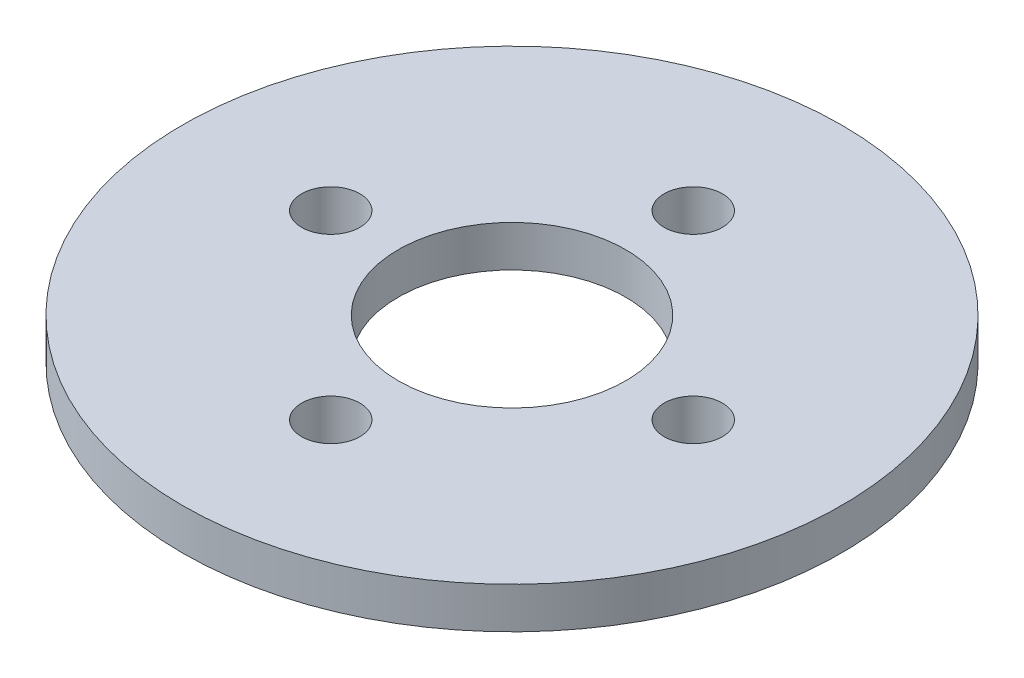
SolidWorks part; units mm, degrees
ref_plane "Front Plane" through (0, 0, 0) normal (0, 0, 1) x (1, 0, 0)
ref_plane "Top Plane" through (0, 0, 0) normal (0, 1, 0) x (1, 0, 0)
ref_plane "Right Plane" through (0, 0, 0) normal (1, 0, 0) x (0, 0, -1)
sketch "Sketch1" plane through (0, 0, 0) normal (0, 1, 0) x (1, 0, 0)
  circle A0 centre (0, 0) radius 25.4
  circle A1 centre (0, 0) radius 8.763
  dimension "D1" = 50.8
  dimension "D2" = 17.526
extrude "Boss-Extrude1" add sketch "Sketch1" along normal blind 3.175
hole_wizard "#8 Clearance Hole1" positions "Sketch2" profile "Sketch3" hole size "#8" standard "ANSI Inch" end condition through all
sketch "Sketch2" plane through (0, 3.175, 0) normal (0, 1, 0) x (1, 0, 0)
  circle A0 centre (0, 0) radius 13.97
  point P4 (0, 13.97)
  point P6 (-13.97, 0)
  point P8 (0, -13.97)
  point P10 (13.97, 0)
  dimension "D1" = 27.94
sketch "Sketch3" plane through (13.97, 3.175, 0) normal (1, 0, 0) x (0, 0, 1)
  line L0 (0, 0) -> (0, 3.175)
  line L1 (0, 3.175) -> (2.2479, 3.175)
  line L2 (2.2479, 3.175) -> (2.2479, 0)
  line L5 (2.2479, 0) -> (0, 0)
  line L11 (0, -6.35) -> (0, 107.95) construction
  dimension "Thru Hole Dia." = 4.4958
  dimension "Thru Hole Depth" = 3.175
equation "\"inner_circle\" = 0.690"
equation "\"D2@Sketch1\"=\"inner_circle\""
